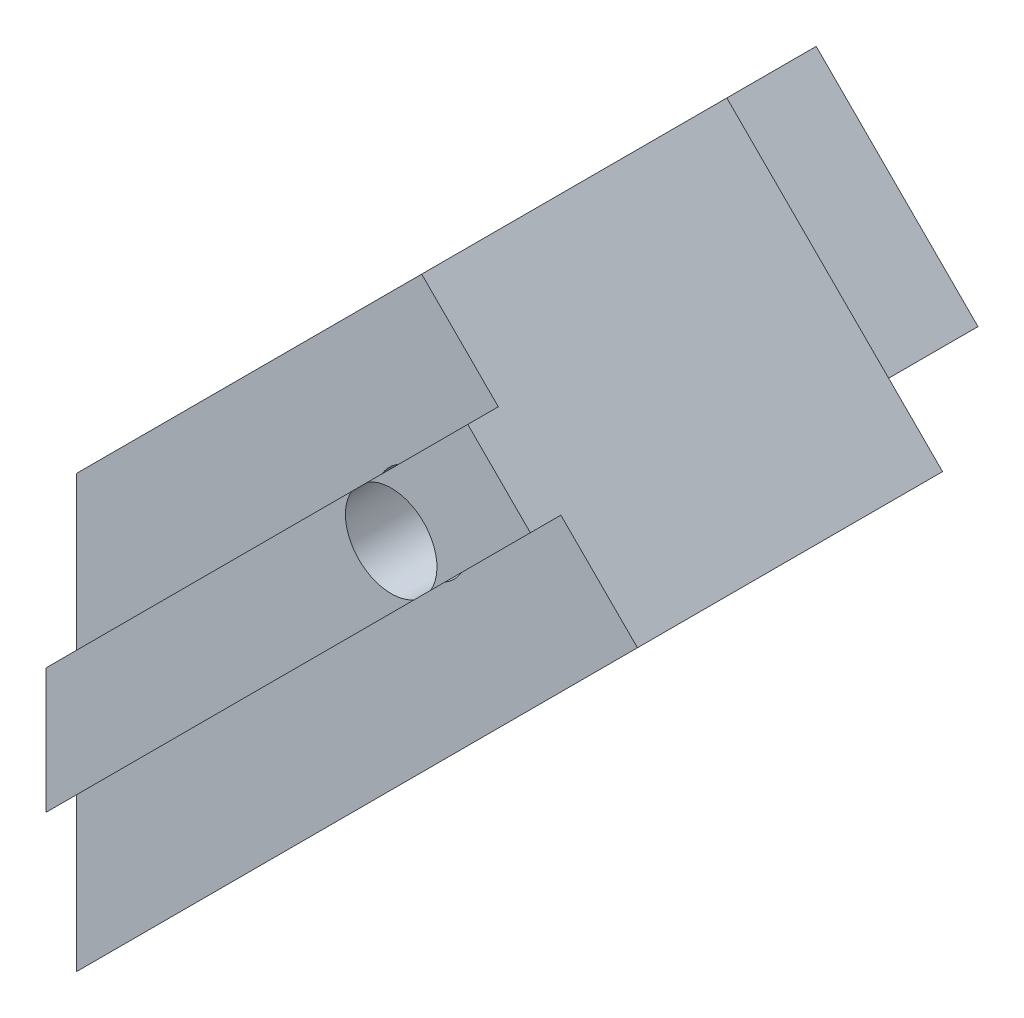
SolidWorks part; units mm, degrees
ref_plane "Front Plane" through (0, 0, 0) normal (0, 0, 1) x (1, 0, 0)
ref_plane "Top Plane" through (0, 0, 0) normal (0, 1, 0) x (1, 0, 0)
ref_plane "Right Plane" through (0, 0, 0) normal (1, 0, 0) x (0, 0, -1)
sketch "Esquisse1" plane through (0, 0, 0) normal (0, 0, 1) x (1, 0, 0)
  line L0 (0, 0) -> (0, 5)
  line L1 (0, 5) -> (-1, 5)
  line L2 (-1, 5) -> (-1, 7.9)
  line L3 (-1, 7.9) -> (0, 7.9)
  line L4 (0, 7.9) -> (0, 14.1421)
  line L5 (0, 14.1421) -> (11.3137, 25.4558)
  line L6 (11.3137, 25.4558) -> (18.3848, 18.3848)
  line L7 (18.3848, 18.3848) -> (0, 0)
  dimension "D1" = 2.9
  dimension "D2" = 45
  dimension "D3" = 10
  dimension "D4" = 5
  dimension "D5" = 1
  dimension "D6" = 26
extrude "Boss.-Extru.1" add sketch "Esquisse1" along normal blind 20
sketch "Esquisse2" plane through (0, 0, 0) normal (0.7071, -0.7071, 0) x (0, 0, -1)
  line L0 (0, 0) -> (0, 26) construction
  line L1 (-10, 5) -> (0, 5)
  line L2 (-10, 5) -> (-10, 26)
  line L3 (-10, 26) -> (0, 26)
  line L4 (0, 5) -> (0, 26)
  line L5 (-20, 26) -> (0, 26) construction
  line L6 (-20, 0) -> (0, 0) construction
  dimension "D1" = 5
  dimension "D2" = 10
extrude "Enlèv. mat.-Extru.1" cut sketch "Esquisse2" against normal blind 2.5
sketch "Esquisse3" plane through (-1, 0, 0) normal (-1, 0, 0) x (0, 0, 1)
  line L0 (20, 7.9) -> (20, 5) construction
  line L2 (20, 7.9) -> (0, 7.9) construction
  circle A0 centre (15, 6.45) radius 1.5
  point P5 (20, 6.45)
  dimension "D1" = 3
  dimension "D2" = 5
extrude "Enlèv. mat.-Extru.2" cut sketch "Esquisse3" against normal through all
ref_plane "Plan1" through (3, 0, 0) normal (-1, 0, 0) x (0, 0, 1)
sketch "Esquisse4" plane through (3, 0, 0) normal (-1, 0, 0) x (0, 0, 1)
  circle A0 centre (15, 6.45) radius 4.1
  arc A1 (15.3841, 5) -> (15.3841, 7.9) centre (15, 6.45) ccw construction
  dimension "D1" = 8.2
extrude "Enlèv. mat.-Extru.3" cut sketch "Esquisse4" against normal through all
sketch "Esquisse5" plane through (-1.7678, 1.7678, 0) normal (0.7071, -0.7071, 0) x (0, 0, -1)
  line L0 (0, 26) -> (-10, 26) construction
  line L2 (-10, 5) -> (0, 5) construction
  circle A0 centre (-5, 11.5) radius 1.25
  point P4 (-5, 26)
  dimension "D1" = 2.5
  dimension "D2" = 6.5
extrude "Enlèv. mat.-Extru.4" cut sketch "Esquisse5" against normal through all
sketch "Esquisse6" plane through (0, 0, 20) normal (0, 0, 1) x (1, 0, 0)
  line L0 (0, 9.1217) -> (13.8239, 22.9456)
  line L1 (18.3848, 18.3848) -> (11.3137, 25.4558) construction
  line L2 (13.8239, 22.9456) -> (15.8745, 20.895)
  line L3 (15.8745, 20.895) -> (0, 5.0205)
  line L4 (0, 5.0205) -> (0, 9.1217)
  line L5 (0, 5) -> (0, 0) construction
  point P6 (14.8492, 21.9203)
  point P7 (14.8492, 21.9203)
  dimension "D1" = 2.9
extrude "Boss.-Extru.2" add sketch "Esquisse6" along normal blind 1
ref_plane "Plan3" through (0, 0, 17) normal (0, 0, 1) x (1, 0, 0)
sketch "Esquisse9" plane through (0, 0, 10) normal (0, 0, -1) x (-1, 0, 0)
  line L0 (-18.3848, 18.3848) -> (-12.0208, 12.0208)
  line L1 (-18.3848, 18.3848) -> (-3.5355, 3.5355) construction
  line L2 (-12.0208, 12.0208) -> (-4.9497, 19.0919)
  line L3 (-4.9497, 19.0919) -> (-11.3137, 25.4558)
  line L5 (-11.3137, 25.4558) -> (-18.3848, 18.3848)
  dimension "D1" = 9
extrude "Enlèv. mat.-Extru.7" cut sketch "Esquisse9" along normal through all
sketch "Esquisse10" plane through (0, 0, 10) normal (0, 0, -1) x (-1, 0, 0)
  line L0 (-11.3137, 25.4558) -> (-4.2426, 18.3848)
  line L1 (-4.2426, 18.3848) -> (-11.3137, 11.3137)
  line L2 (-18.3848, 18.3848) -> (-3.5355, 3.5355) construction
  line L3 (-11.3137, 11.3137) -> (-18.3848, 18.3848)
  line L4 (-18.3848, 18.3848) -> (-11.3137, 25.4558)
  dimension "D1" = 10
extrude "Enlèv. mat.-Extru.8" cut sketch "Esquisse10" along normal through all
sketch "Esquisse11" plane through (0, 0, 10) normal (0, 0, -1) x (-1, 0, 0)
  line L0 (-18.3848, 18.3848) -> (-3.5355, 3.5355) construction
  line L1 (-11.3137, 25.4558) -> (-18.3848, 18.3848) construction
  circle A0 centre (-11.3137, 18.3848) radius 1.5
  dimension "D1" = 3
  dimension "D2" = 5
  dimension "D3" = 5
extrude "Enlèv. mat.-Extru.9" cut sketch "Esquisse11" against normal through all
sketch "Esquisse12" plane through (0, 0, 10) normal (0, 0, -1) x (-1, 0, 0)
  circle A0 centre (-11.3137, 18.3848) radius 4.1
  circle A1 centre (-11.3137, 18.3848) radius 1.5 construction
  dimension "D1" = 8.2
extrude "Enlèv. mat.-Extru.10" cut sketch "Esquisse12" against normal blind 7.5
ref_plane "SymetryPlan" through (19.799, 19.799, 0) normal (0.7071, 0.7071, 0) x (0.7071, -0.7071, 0)
